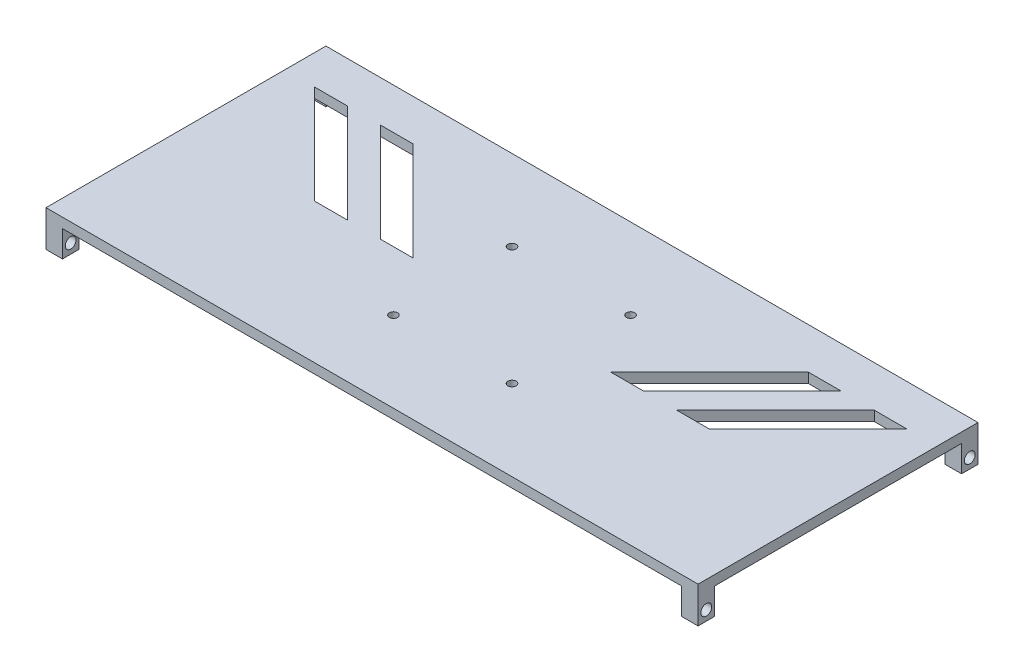
SolidWorks part; units mm, degrees
ref_plane "前视基准面" through (0, 0, 0) normal (0, 0, 1) x (1, 0, 0)
ref_plane "上视基准面" through (0, 0, 0) normal (0, 1, 0) x (1, 0, 0)
ref_plane "右视基准面" through (0, 0, 0) normal (1, 0, 0) x (0, 0, -1)
sketch "草图1" plane through (0, 0, 0) normal (0, 1, 0) x (1, 0, 0)
  line L1 (-99, -42.5) -> (99, -42.5)
  line L2 (-99, -42.5) -> (-99, 42.5)
  line L3 (-99, 42.5) -> (99, 42.5)
  line L4 (99, -42.5) -> (99, 42.5)
  line L5 (-99, -42.5) -> (99, 42.5) construction
  line L6 (-99, 42.5) -> (99, -42.5) construction
  point P0 (0, 0)
  dimension "D1" = 85
  dimension "D2" = 198
extrude "凸台-拉伸1" add sketch "草图1" along normal blind 3 contours L1 L4 L3 L2
sketch "草图3" plane through (-99, 0, 0) normal (-1, 0, 0) x (0, 0, 1)
  line L0 (0, 0) -> (40, 0)
  line L1 (42.5, 0) -> (-42.5, 0) construction
  line L2 (0, 0) -> (-40, 0)
  line L3 (-40, 0) -> (-40, -5)
  line L5 (-42.5, 0) -> (-37.5027, 0)
  line L6 (-42.5, 0) -> (-42.5, -8)
  line L7 (-42.5, -8) -> (-37.5027, -8)
  line L8 (-37.5027, 0) -> (-37.5027, -8)
  line L9 (40, 0) -> (40, -5)
  line L11 (42.5, 0) -> (37.5, 0)
  line L12 (42.5, 0) -> (42.5, -8)
  line L13 (42.5, -8) -> (37.5, -8)
  line L14 (37.5, 0) -> (37.5, -8)
  circle A0 centre (-40, -5) radius 1.65
  circle A1 centre (40, -5) radius 1.65
  dimension "D4" = 3.3
  dimension "D7" = 3.3
  dimension "D1" = 40
  dimension "D2" = 40
  dimension "D3" = 5
  dimension "D5" = 4.9973
  dimension "D6" = 8
  dimension "D8" = 5
  dimension "D9" = 8
extrude "凸台-拉伸2" add sketch "草图3" against normal blind 5
sketch "草图4" plane through (99, 0, 0) normal (1, 0, 0) x (0, 0, -1)
  line L0 (0, 0) -> (-40, 0)
  line L1 (55, 0) -> (-55, 0) construction
  line L2 (0, 0) -> (40, 0)
  line L3 (-40, 0) -> (-40, -5)
  line L4 (-42.5, 0) -> (-42.5, -8) construction
  line L5 (-42.5, 0) -> (-37.5, 0)
  line L6 (-42.5, 0) -> (-42.5, -8)
  line L7 (-42.5, -8) -> (-37.5, -8)
  line L8 (-37.5, 0) -> (-37.5, -8)
  line L9 (40, 0) -> (40, -5)
  line L10 (42.5, 0) -> (42.5, -8) construction
  line L11 (42.5, 0) -> (37.5, 0)
  line L12 (42.5, 0) -> (42.5, -8)
  line L13 (42.5, -8) -> (37.5, -8)
  line L14 (37.5, 0) -> (37.5, -8)
  circle A0 centre (-40, -5) radius 1.65
  circle A1 centre (40, -5) radius 1.65
  dimension "D4" = 3.3
  dimension "D8" = 3.3
  dimension "D1" = 40
  dimension "D2" = 40
  dimension "D3" = 5
  dimension "D5" = 5
  dimension "D6" = 8
  dimension "D7" = 5
  dimension "D9" = 5
  dimension "D10" = 8
extrude "凸台-拉伸3" add sketch "草图4" against normal blind 5
sketch "草图5" plane through (0, 3, 0) normal (0, 1, 0) x (1, 0, 0)
  line L1 (-18, -18) -> (18, -18) construction
  line L2 (-18, -18) -> (-18, 18) construction
  line L3 (-18, 18) -> (18, 18) construction
  line L4 (18, -18) -> (18, 18) construction
  line L5 (-18, -18) -> (18, 18) construction
  line L6 (-18, 18) -> (18, -18) construction
  circle A0 centre (-18, 18) radius 1.25
  circle A1 centre (-18, -18) radius 1.25
  circle A2 centre (18, -18) radius 1.25
  circle A3 centre (18, 18) radius 1.25
  point P0 (0, 0)
  point P16 (0, 0)
  dimension "D3" = 2.5
  dimension "D1" = 36
  dimension "D2" = 36
  dimension "D4" = 4
extrude "切除-拉伸1" cut sketch "草图5" against normal blind 10
sketch "草图6" plane through (0, 3, 0) normal (0, 1, 0) x (1, 0, 0)
  line L0 (60, 30) -> (70, 30)
  line L1 (0, 0) -> (-30, 0)
  line L6 (-40, 0) -> (-30, 0)
  line L7 (-30, 0) -> (-60, 30)
  line L8 (-60, 30) -> (-70, 30)
  line L9 (-70, 30) -> (-40, 0)
  line L10 (-60, 0) -> (-50, 0)
  line L11 (-50, 0) -> (-80, 30)
  line L12 (-80, 30) -> (-90, 30)
  line L13 (-90, 30) -> (-60, 0)
  line L14 (0, 0) -> (-50, 0)
  line L15 (0, 0) -> (0, 42.5) construction
  line L16 (-99, 42.5) -> (99, 42.5) construction
  line L17 (30, 0) -> (60, 30)
  line L18 (40, 0) -> (30, 0)
  line L19 (70, 30) -> (40, 0)
  line L20 (80, 30) -> (90, 30)
  line L21 (50, 0) -> (80, 30)
  line L22 (60, 0) -> (50, 0)
  line L23 (90, 30) -> (60, 0)
  dimension "D1" = 30
  dimension "D3" = 135
  dimension "D4" = 30
  dimension "D5" = 10
  dimension "D6" = 10
  dimension "D7" = 10
  dimension "D8" = 30
  dimension "D9" = 135
  dimension "D10" = 50
extrude "切除-拉伸2" cut sketch "草图6" against normal blind 3 contours L13 L10 L11 L12 | L9 L6 L7 L8 | L19 L18 L17 L0 | L23 L22 L21 L20
